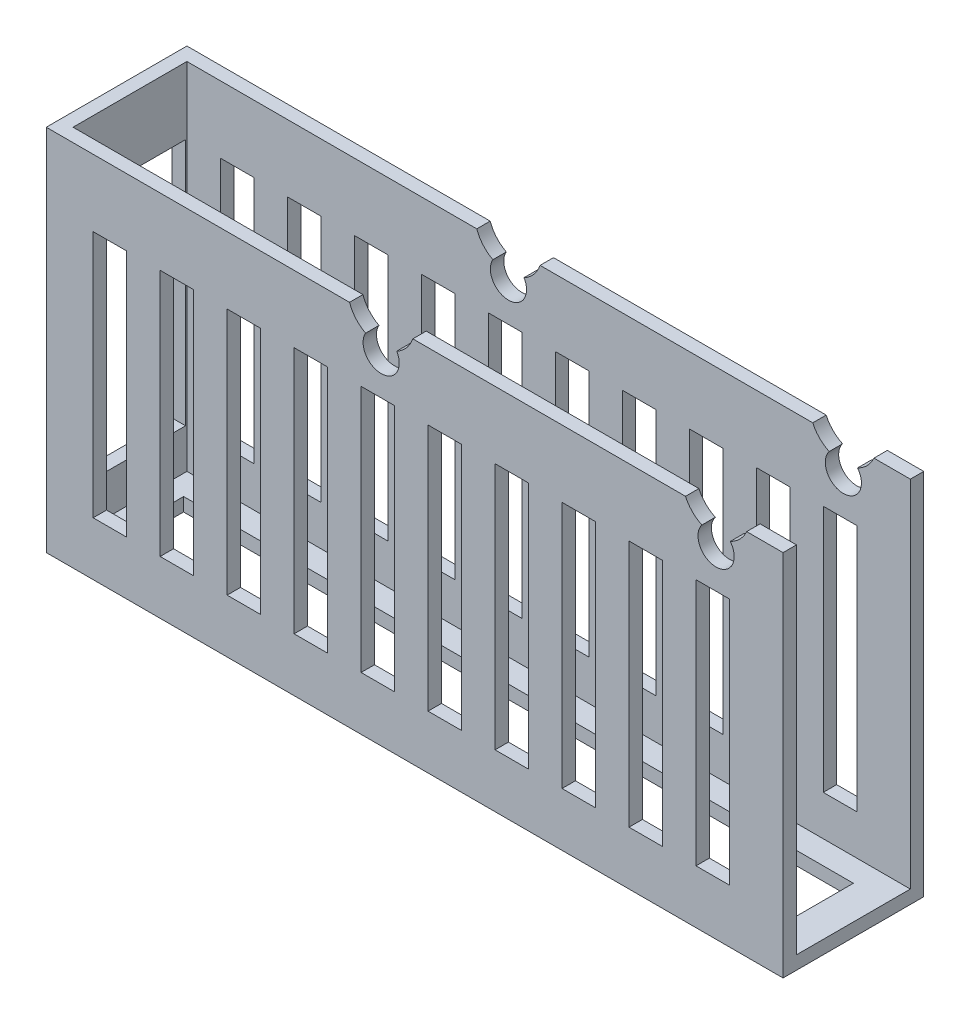
SolidWorks part; units mm, degrees
ref_plane "前视基准面" through (0, 0, 0) normal (0, 0, 1) x (1, 0, 0)
ref_plane "上视基准面" through (0, 0, 0) normal (0, 1, 0) x (1, 0, 0)
ref_plane "右视基准面" through (0, 0, 0) normal (1, 0, 0) x (0, 0, -1)
sketch "草图1" plane through (0, 0, 0) normal (0, 1, 0) x (1, 0, 0)
  line L1 (-55, 10.5) -> (55, 10.5)
  line L2 (-55, 10.5) -> (-55, -10.5)
  line L3 (-55, -10.5) -> (55, -10.5)
  line L4 (55, 10.5) -> (55, -10.5)
  line L5 (-55, 10.5) -> (55, -10.5) construction
  line L6 (-55, -10.5) -> (55, 10.5) construction
  point P0 (0, 0)
  dimension "D1" = 21
  dimension "D2" = 110
extrude "凸台-拉伸1" add sketch "草图1" along normal blind 55
sketch "草图5" plane through (0, 0, -10.5) normal (0, 0, -1) x (-1, 0, 0)
  arc A9 (-47.1202, 52.5109) -> (-42.8798, 52.5109) centre (-45, 50.8391) ccw
  arc A10 (-42.8798, 52.5109) -> (-47.1202, 52.5109) centre (-45, 57.0391) ccw
  arc A11 (2.6752, 52.2121) -> (7.3248, 52.2121) centre (5, 50.8391) ccw
  arc A12 (7.3248, 52.2121) -> (2.6752, 52.2121) centre (5, 56.6388) ccw
  dimension "D2" = 50
  dimension "D1" = 6.2
shell "抽壳1" thickness 2
sketch "草图2" plane through (55, 0, 0) normal (1, 0, 0) x (0, 0, -1)
  line L1 (-8.5, 55) -> (8.5, 55)
  line L2 (-8.5, 55) -> (-8.5, 2)
  line L3 (-8.5, 2) -> (8.5, 2)
  line L4 (8.5, 55) -> (8.5, 2)
extrude "切除-拉伸1" cut sketch "草图2" against normal blind 50
sketch "草图8" plane through (0, 0, -10.5) normal (0, 0, -1) x (-1, 0, 0)
  line L0 (-37, 45) -> (-37, 8)
  line L1 (-37, 45) -> (-32, 45)
  line L2 (-55, 55) -> (-55, 0) construction
  line L3 (-47, 45) -> (-42, 45)
  line L4 (-47, 45) -> (-47, 8)
  line L5 (-47, 8) -> (-42, 8)
  line L6 (-42, 45) -> (-42, 8)
  line L8 (-55, 0) -> (55, 0) construction
  line L9 (-55, 55) -> (55, 55) construction
  line L10 (-32, 45) -> (-32, 8)
  line L11 (-37, 8) -> (-32, 8)
  line L12 (-27, 45) -> (-27, 8)
  line L13 (-27, 45) -> (-22, 45)
  line L14 (-22, 45) -> (-22, 8)
  line L15 (-27, 8) -> (-22, 8)
  line L16 (-17, 45) -> (-17, 8)
  line L17 (-17, 45) -> (-12, 45)
  line L18 (-12, 45) -> (-12, 8)
  line L19 (-17, 8) -> (-12, 8)
  line L20 (-7, 45) -> (-7, 8)
  line L21 (-7, 45) -> (-2, 45)
  line L22 (-2, 45) -> (-2, 8)
  line L23 (-7, 8) -> (-2, 8)
  line L24 (3, 45) -> (3, 8)
  line L25 (3, 45) -> (8, 45)
  line L26 (8, 45) -> (8, 8)
  line L27 (3, 8) -> (8, 8)
  line L28 (13, 45) -> (13, 8)
  line L29 (13, 45) -> (18, 45)
  line L30 (18, 45) -> (18, 8)
  line L31 (13, 8) -> (18, 8)
  line L32 (23, 45) -> (23, 8)
  line L33 (23, 45) -> (28, 45)
  line L34 (28, 45) -> (28, 8)
  line L35 (23, 8) -> (28, 8)
  line L36 (33, 45) -> (33, 8)
  line L37 (33, 45) -> (38, 45)
  line L38 (38, 45) -> (38, 8)
  line L39 (33, 8) -> (38, 8)
  line L40 (43, 45) -> (43, 8)
  line L41 (43, 45) -> (48, 45)
  line L42 (48, 45) -> (48, 8)
  line L43 (43, 8) -> (48, 8)
  dimension "D1" = 8
  dimension "D2" = 5
  dimension "D3" = 8
  dimension "D4" = 10
  dimension "D5" = 10
extrude "切除-拉伸8" cut sketch "草图8" against normal through all
sketch "草图9" plane through (-55, 0, 0) normal (-1, 0, 0) x (0, 0, 1)
  line L0 (-10.5, 0) -> (10.5, 0) construction
  line L1 (-8.2973, 45) -> (8.5206, 45)
  line L2 (-8.2973, 45) -> (-8.2973, 8)
  line L3 (-8.2973, 8) -> (8.5206, 8)
  line L4 (8.5206, 45) -> (8.5206, 8)
  dimension "D1" = 37
  dimension "D2" = 8
extrude "切除-拉伸9" cut sketch "草图9" against normal through all
sketch "草图10" plane through (0, 0, 0) normal (0, -1, 0) x (1, 0, 0)
  line L1 (-50, 5) -> (50, 5)
  line L2 (-50, 5) -> (-50, -5)
  line L3 (-50, -5) -> (50, -5)
  line L4 (50, 5) -> (50, -5)
  line L5 (-50, 5) -> (50, -5) construction
  line L6 (-50, -5) -> (50, 5) construction
  point P0 (0, 0)
  dimension "D1" = 10
  dimension "D2" = 100
extrude "切除-拉伸10" cut sketch "草图10" against normal through all
extrude "切除-拉伸11" cut sketch "草图5" against normal through all
